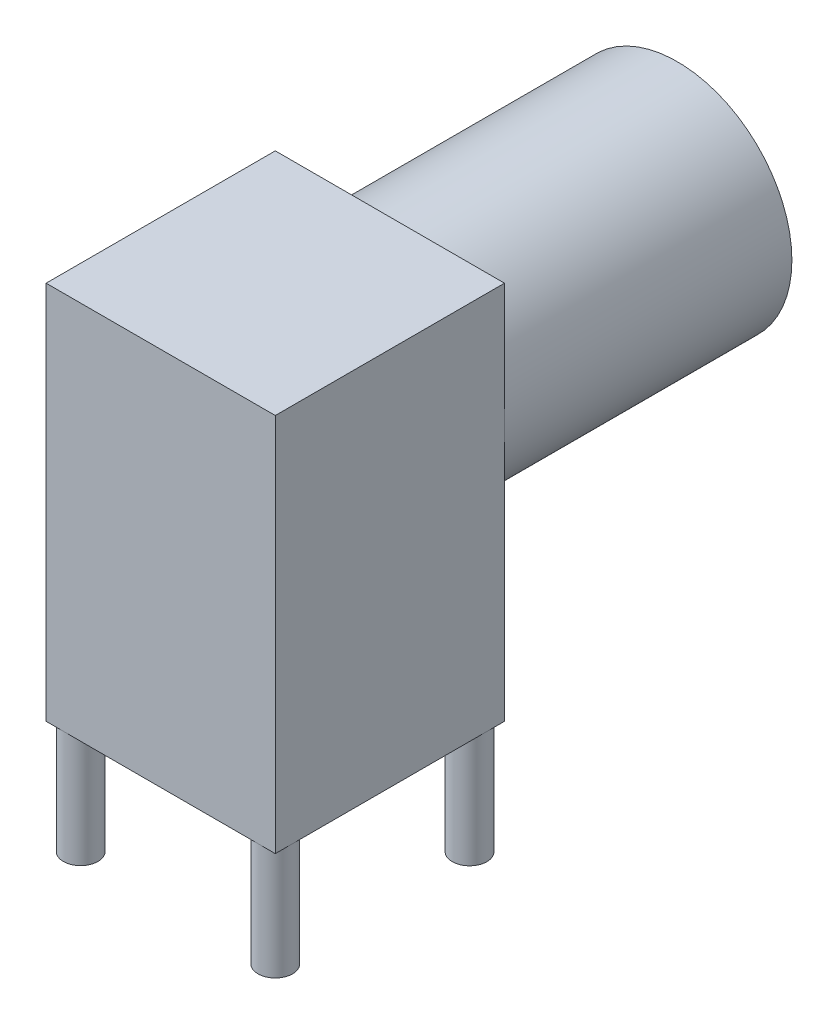
SolidWorks part; units mm, degrees
ref_plane "Front Plane" through (0, 0, 0) normal (0, 0, 1) x (1, 0, 0)
ref_plane "Top Plane" through (0, 0, 0) normal (0, 1, 0) x (1, 0, 0)
ref_plane "Right Plane" through (0, 0, 0) normal (1, 0, 0) x (0, 0, -1)
sketch "Sketch1" plane through (0, 0, 0) normal (0, 1, 0) x (1, 0, 0)
  line L1 (3.15, -3.15) -> (-3.15, -3.15)
  line L2 (3.15, -3.15) -> (3.15, 3.15)
  line L3 (3.15, 3.15) -> (-3.15, 3.15)
  line L4 (-3.15, -3.15) -> (-3.15, 3.15)
  line L5 (3.15, -3.15) -> (-3.15, 3.15) construction
  line L6 (3.15, 3.15) -> (-3.15, -3.15) construction
  point P0 (0, 0)
  dimension "D1" = 6.3
  dimension "D2" = 6.3
extrude "Boss-Extrude1" add sketch "Sketch1" along normal blind 10.43
sketch "Sketch2" plane through (0, 0, -3.15) normal (0, 0, -1) x (-1, 0, 0)
  circle A0 centre (0, 7.0292) radius 3.15
extrude "Boss-Extrude2" add sketch "Sketch2" along normal blind 7.9
sketch "Sketch3" plane through (0, 0, 0) normal (0, -1, 0) x (-1, 0, 0)
  line L0 (3.15, -3.15) -> (-3.15, -3.15) construction
  line L1 (3.15, 3.15) -> (3.15, -3.15) construction
  line L2 (-3.15, -3.15) -> (-3.15, 3.15) construction
  circle A0 centre (0, 0) radius 0.475
  circle A1 centre (2.675, -2.675) radius 0.475
  circle A2 centre (-2.675, -2.675) radius 0.475
  circle A3 centre (2.675, 2.6652) radius 0.475
  circle A4 centre (-2.675, 2.6652) radius 0.475
extrude "Boss-Extrude3" add sketch "Sketch3" along normal blind 3.1
